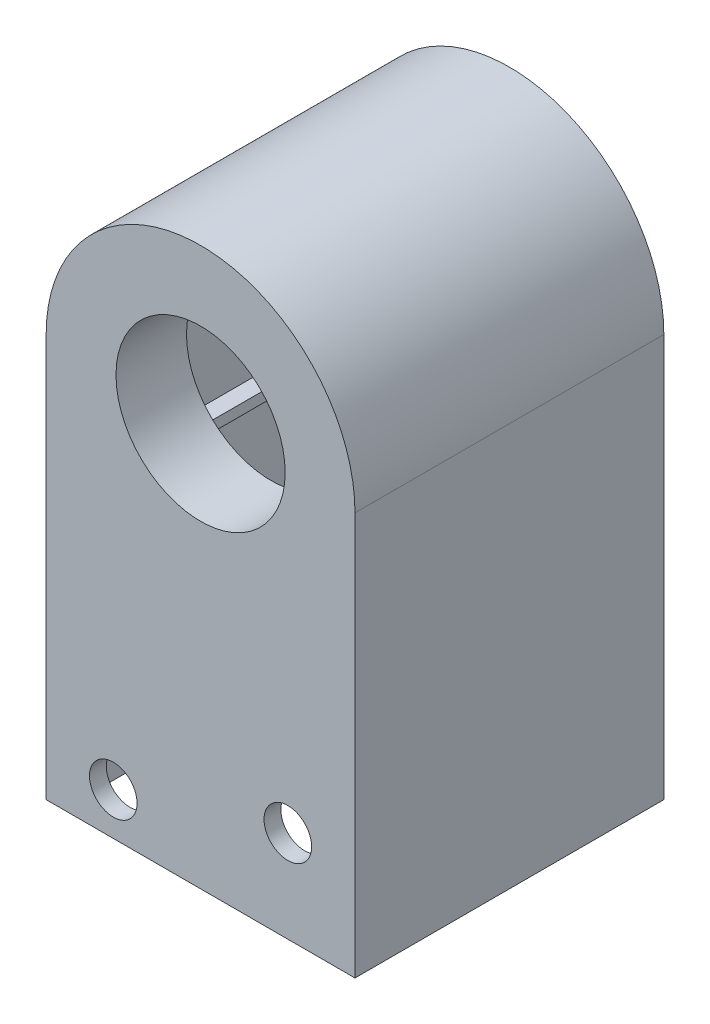
SolidWorks part; units mm, degrees
ref_plane "Front Plane" through (0, 0, 0) normal (0, 0, 1) x (1, 0, 0)
ref_plane "Top Plane" through (0, 0, 0) normal (0, 1, 0) x (1, 0, 0)
ref_plane "Right Plane" through (0, 0, 0) normal (1, 0, 0) x (0, 0, -1)
sketch "Sketch1" plane through (0, 0, 0) normal (0, 1, 0) x (1, 0, 0)
  line L0 (14.605, 14.605) -> (-14.605, 14.605)
  line L1 (13.0175, -13.0175) -> (-13.0175, -13.0175)
  line L2 (13.0175, -13.0175) -> (13.0175, 13.0175)
  line L3 (13.0175, 13.0175) -> (-13.0175, 13.0175)
  line L4 (-13.0175, -13.0175) -> (-13.0175, 13.0175)
  line L5 (13.0175, -13.0175) -> (-13.0175, 13.0175) construction
  line L6 (13.0175, 13.0175) -> (-13.0175, -13.0175) construction
  line L7 (-14.605, -14.605) -> (-14.605, 14.605)
  line L8 (14.605, -14.605) -> (-14.605, -14.605)
  line L9 (14.605, -14.605) -> (14.605, 14.605)
  point P0 (0, 0)
  dimension "D1" = 26.035
  dimension "D2" = 1.5875
extrude "Boss-Extrude1" add sketch "Sketch1" along normal blind 101.6
sketch "Sketch2" plane through (0, 0, 14.605) normal (0, 0, 1) x (1, 0, 0)
  line L2 (-14.605, 0) -> (14.605, 0) construction
  line L6 (-14.605, 0) -> (14.605, 0)
  line L7 (14.605, 0) -> (14.605, 101.6)
  line L8 (14.605, 101.6) -> (-14.605, 101.6)
  line L9 (-14.605, 101.6) -> (-14.605, 0)
  line L10 (-14.605, 0) -> (14.605, 0)
  line L11 (14.605, 0) -> (14.605, 101.6)
  line L12 (14.605, 101.6) -> (-14.605, 101.6)
  line L13 (-14.605, 101.6) -> (-14.605, 0)
  circle A0 centre (0, 38.1) radius 8
  circle A1 centre (0, 38.1) radius 14.605
  line M3 (14.605, 101.6) -> (-14.605, 101.6)
  line M4 (-14.605, 101.6) -> (-14.605, 0)
  dimension "D1" = 16
  dimension "D3" = 38.1
  dimension "D2" = 0
extrude "Cut-Extrude1" cut sketch "Sketch2" against normal blind 50.8 contours A1 L11 M3 M4 | A0
sketch "Sketch5" plane through (0, 0, -13.0175) normal (0, 0, 1) x (1, 0, 0)
  line L0 (-13.0175, 44.722) -> (-13.0175, 0) construction
  line L1 (-13.0175, 44.722) -> (-13.0175, 38.1) construction
  line L2 (-14.605, 38.1) -> (14.605, 38.1)
  arc A0 (14.605, 38.1) -> (-14.605, 38.1) centre (0, 38.1) ccw construction
  arc A1 (14.605, 38.1) -> (-14.605, 38.1) centre (0, 38.1) ccw
  arc A2 (13.0175, 38.1) -> (-13.0175, 38.1) centre (0, 38.1) ccw
  line M3 (13.0175, 0) -> (13.0175, 44.722)
  arc M4 (13.0175, 44.722) -> (-13.0175, 44.722) centre (0, 38.1) ccw
  line M5 (-13.0175, 44.722) -> (-13.0175, 0)
extrude "Boss-Extrude2" add sketch "Sketch5" along normal up to surface (26.035 mm away) contours A2 M3 M4 M5 up to face at (-8, 38.1, 13.0175)
sketch "Sketch6" plane through (0, 0, 13.0175) normal (0, 0, -1) x (-1, 0, 0)
  line L0 (-13.0175, 25.4) -> (13.0175, 25.4)
  line L1 (-13.0175, 38.1) -> (-13.0175, 0) construction
  line L2 (13.0175, 38.1) -> (13.0175, 0) construction
  circle A0 centre (0, 38.1) radius 8 construction
  circle A1 centre (0, 38.1) radius 8
  circle A2 centre (0, 38.1) radius 10.16
  circle M2 centre (0, 38.1) radius 8
  dimension "D2" = 20.32
  dimension "D1" = 12.7
extrude "Boss-Extrude3" add sketch "Sketch6" along normal blind 5.08 contours A2 M2
fillet "Fillet1" radius 2.54 1 edges at (-10.16, 38.1, 13.0175)
mirror "Mirror7" about plane through (0, 0, 0) normal (0, 0, 1) of bodies 104
sketch "Sketch7" plane through (0, 0, -14.605) normal (0, 0, -1) x (-1, 0, 0)
  line L0 (-14.605, 12.7) -> (14.605, 12.7) construction
  line L1 (-14.605, 38.1) -> (-14.605, 0) construction
  line L2 (14.605, 38.1) -> (14.605, 0) construction
  line L3 (-14.605, 0) -> (14.605, 0) construction
  circle A0 centre (-8.255, 8.7) radius 2.25
  circle A1 centre (8.255, 4) radius 2.25
  dimension "D1" = 4.5
  dimension "D2" = 12.7
  dimension "D3" = 4
  dimension "D4" = 6.35
  dimension "D5" = 6.35
  dimension "D6" = 4
extrude "Cut-Extrude2" cut sketch "Sketch7" against normal blind 46.736
ref_plane "Plane1" through (0, 25.4, 0) normal (0, -1, 0) x (-1, 0, 0)
sketch "Sketch8" plane through (0, 25.4, 0) normal (0, -1, 0) x (-1, 0, 0)
  line L1 (11.43, -11.43) -> (-11.43, -11.43)
  line L2 (11.43, -11.43) -> (11.43, 11.43)
  line L3 (11.43, 11.43) -> (-11.43, 11.43)
  line L4 (-11.43, -11.43) -> (-11.43, 11.43)
  line L5 (11.43, -11.43) -> (-11.43, 11.43) construction
  line L6 (11.43, 11.43) -> (-11.43, -11.43) construction
  line L10 (13.0175, -13.0175) -> (13.0175, 13.0175)
  line L22 (13.0175, -13.0175) -> (13.0175, 13.0175)
  line L26 (-13.0175, -13.0175) -> (13.0175, -13.0175)
  line L28 (-13.0175, -13.0175) -> (13.0175, -13.0175)
  line L30 (-13.0175, 13.0175) -> (-13.0175, -13.0175)
  line L31 (-13.0175, 13.0175) -> (-13.0175, -13.0175)
  line L32 (13.0175, 13.0175) -> (-13.0175, 13.0175)
  line L33 (13.0175, 13.0175) -> (-13.0175, 13.0175)
  point P0 (0, 0)
  dimension "D1" = 22.86
  dimension "D2" = 0
extrude "Boss-Extrude4" add sketch "Sketch8" against normal blind 1
